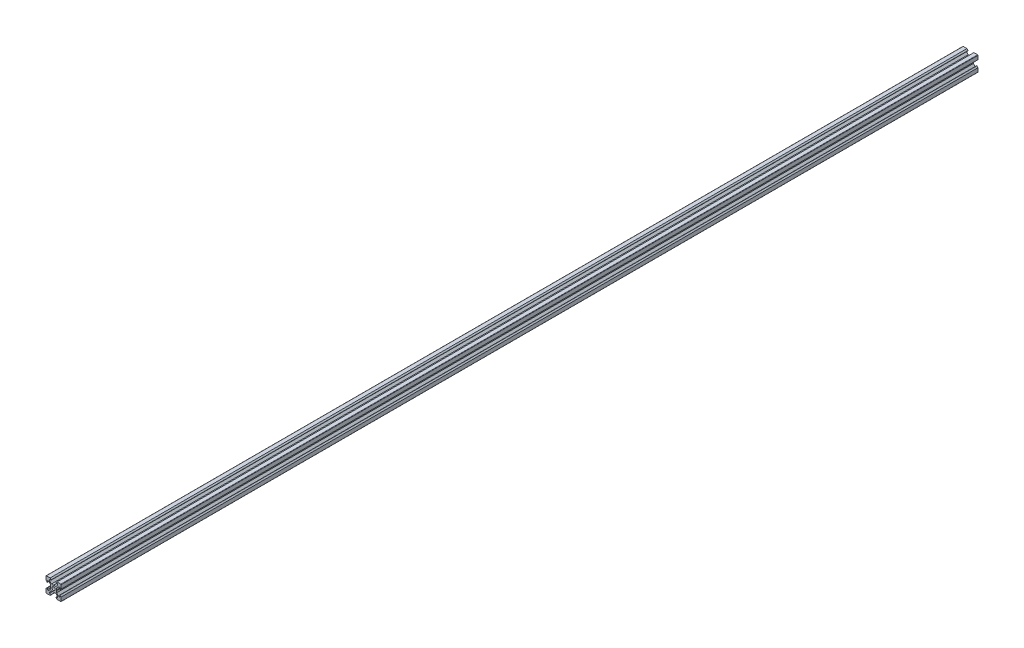
SolidWorks part; units mm, degrees
material "6061-T6 (SS)"
ref_plane "Front Plane" through (0, 0, 0) normal (0, 0, 1) x (1, 0, 0)
ref_plane "Top Plane" through (0, 0, 0) normal (0, 1, 0) x (1, 0, 0)
ref_plane "Right Plane" through (0, 0, 0) normal (1, 0, 0) x (0, 0, -1)
sketch "Sketch1" plane through (0, 0, 0) normal (0, 0, 1) x (1, 0, 0)
  line L1 (9.5, -10) -> (-9.5, -10)
  line L2 (10, -9.5) -> (10, 9.5)
  line L3 (9.5, 10) -> (-9.5, 10)
  line L4 (-10, -9.5) -> (-10, 9.5)
  line L5 (10, -10) -> (-10, 10) construction
  line L6 (10, 10) -> (-10, -10) construction
  circle A0 centre (0, 0) radius 2.1
  arc A1 (-9.5, 10) -> (-10, 9.5) centre (-9.5, 9.5) ccw
  arc A2 (10, 9.5) -> (9.5, 10) centre (9.5, 9.5) ccw
  arc A3 (9.5, -10) -> (10, -9.5) centre (9.5, -9.5) ccw
  arc A4 (-9.5, -10) -> (-10, -9.5) centre (-9.5, -9.5) cw
  point P0 (0, 0)
  line B0 (0, 0) -> (0, 10) construction
  line B1 (0, 3.69) -> (-0.21, 3.9)
  line B2 (-0.21, 3.9) -> (-2.8393, 3.9)
  line B3 (-2.8393, 3.9) -> (-5.5, 6.5607)
  line B4 (-5.5, 6.5607) -> (-5.5, 8.2)
  line B5 (-5.5, 8.2) -> (-3.125, 8.2)
  line B6 (-3.125, 8.2) -> (-3.125, 8.545)
  line B7 (-3.125, 8.545) -> (-4.58, 10)
  line B8 (-4.58, 10) -> (4.58, 10)
  line B9 (0, 0) -> (-5.9132, 5.9132) construction
  line B10 (3.125, 8.545) -> (4.58, 10)
  line B11 (3.125, 8.2) -> (3.125, 8.545)
  line B12 (5.5, 8.2) -> (3.125, 8.2)
  line B13 (5.5, 6.5607) -> (5.5, 8.2)
  line B14 (2.8393, 3.9) -> (5.5, 6.5607)
  line B15 (0.21, 3.9) -> (2.8393, 3.9)
  line B16 (0, 3.69) -> (0.21, 3.9)
  line B17 (0, 0) -> (-10, 0) construction
  line B18 (-3.69, 0) -> (-3.9, -0.21)
  line B19 (-3.9, -0.21) -> (-3.9, -2.8393)
  line B20 (-3.9, -2.8393) -> (-6.5607, -5.5)
  line B21 (-6.5607, -5.5) -> (-8.2, -5.5)
  line B22 (-8.2, -5.5) -> (-8.2, -3.125)
  line B23 (-8.2, -3.125) -> (-8.545, -3.125)
  line B24 (-8.545, -3.125) -> (-10, -4.58)
  line B25 (-10, -4.58) -> (-10, 4.58)
  line B26 (0, 0) -> (-5.9132, -5.9132) construction
  line B27 (-8.545, 3.125) -> (-10, 4.58)
  line B28 (-8.2, 3.125) -> (-8.545, 3.125)
  line B29 (-8.2, 5.5) -> (-8.2, 3.125)
  line B30 (-6.5607, 5.5) -> (-8.2, 5.5)
  line B31 (-3.9, 2.8393) -> (-6.5607, 5.5)
  line B32 (-3.9, 0.21) -> (-3.9, 2.8393)
  line B33 (-3.69, 0) -> (-3.9, 0.21)
  line B34 (0, 0) -> (0, -10) construction
  line B35 (0, -3.69) -> (0.21, -3.9)
  line B36 (0.21, -3.9) -> (2.8393, -3.9)
  line B37 (2.8393, -3.9) -> (5.5, -6.5607)
  line B38 (5.5, -6.5607) -> (5.5, -8.2)
  line B39 (5.5, -8.2) -> (3.125, -8.2)
  line B40 (3.125, -8.2) -> (3.125, -8.545)
  line B41 (3.125, -8.545) -> (4.58, -10)
  line B42 (4.58, -10) -> (-4.58, -10)
  line B43 (0, 0) -> (5.9132, -5.9132) construction
  line B44 (-3.125, -8.545) -> (-4.58, -10)
  line B45 (-3.125, -8.2) -> (-3.125, -8.545)
  line B46 (-5.5, -8.2) -> (-3.125, -8.2)
  line B47 (-5.5, -6.5607) -> (-5.5, -8.2)
  line B48 (-2.8393, -3.9) -> (-5.5, -6.5607)
  line B49 (-0.21, -3.9) -> (-2.8393, -3.9)
  line B50 (0, -3.69) -> (-0.21, -3.9)
  line B51 (0, 0) -> (10, 0) construction
  line B52 (3.69, 0) -> (3.9, 0.21)
  line B53 (3.9, 0.21) -> (3.9, 2.8393)
  line B54 (3.9, 2.8393) -> (6.5607, 5.5)
  line B55 (6.5607, 5.5) -> (8.2, 5.5)
  line B56 (8.2, 5.5) -> (8.2, 3.125)
  line B57 (8.2, 3.125) -> (8.545, 3.125)
  line B58 (8.545, 3.125) -> (10, 4.58)
  line B59 (10, 4.58) -> (10, -4.58)
  line B60 (0, 0) -> (5.9132, 5.9132) construction
  line B61 (8.545, -3.125) -> (10, -4.58)
  line B62 (8.2, -3.125) -> (8.545, -3.125)
  line B63 (8.2, -5.5) -> (8.2, -3.125)
  line B64 (6.5607, -5.5) -> (8.2, -5.5)
  line B65 (3.9, -2.8393) -> (6.5607, -5.5)
  line B66 (3.9, -0.21) -> (3.9, -2.8393)
  line B67 (3.69, 0) -> (3.9, -0.21)
  dimension "D1" = 4.2
  dimension "D3" = 0.5
  dimension "D2" = 20
sketch_block_instance "V Slot 1-4"
sketch_block "V Slot 1" parameters "D1"=10, "D2"=11, "D3"=4.3, "D4"=1.8, "D5"=0.21, "D6"=45, "D7"=9.16, "D8"=1.5, "D9"=6.25
sketch_block_instance "V Slot 1-5"
sketch_block_instance "V Slot 1-6"
sketch_block_instance "V Slot 1-7"
extrude "Boss-Extrude1" add sketch "Sketch1" along normal blind 1210 contours B67 B52 B53 B54 B55 B56 B57 B58 L2 A2 L3 B10 B11 B12 B13 B14 B15 B16 B1 B2 B3 B4 B5 B6 B7 A1 L4 B27 B28 B29 B30 B31 B32 B33 B18 B19 B20 B21 B22 B23 B24 A4 L1 B44 B45 B46 B47 B48 B49
